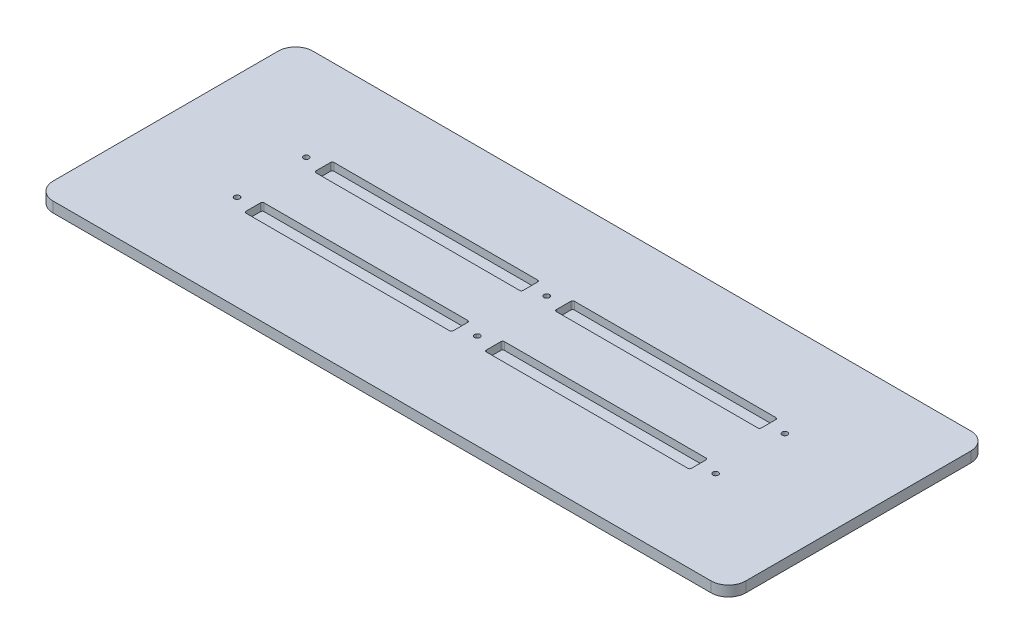
SolidWorks part; units mm, degrees
ref_plane "Ön Düzlem" through (0, 0, 0) normal (0, 0, 1) x (1, 0, 0)
ref_plane "Üst Düzlem" through (0, 0, 0) normal (0, 1, 0) x (1, 0, 0)
ref_plane "Sağ Düzlem" through (0, 0, 0) normal (1, 0, 0) x (0, 0, -1)
sketch "Çizim1" plane through (0, 0, 0) normal (0, 1, 0) x (1, 0, 0)
  line L1 (-200, -75) -> (200, -75)
  line L2 (-200, -75) -> (-200, 75)
  line L3 (-200, 75) -> (200, 75)
  line L4 (200, -75) -> (200, 75)
  line L5 (-200, -75) -> (200, 75) construction
  line L6 (-200, 75) -> (200, -75) construction
  point P0 (0, 0)
  dimension "D1" = 400
  dimension "D2" = 150
extrude "Yükseklik-Ekstrüzyon1" add sketch "Çizim1" against normal blind 6
sketch "Çizim2" plane through (0, 0, 0) normal (0, 1, 0) x (1, 0, 0)
  line L0 (-200, 0) -> (200, 0) construction
  line L1 (-200, 75) -> (-200, -75) construction
  line L2 (200, -75) -> (200, 75) construction
  line L3 (127.99, -15) -> (147.19, -25.4) construction
  line L4 (200, 75) -> (-200, 75) construction
  line L5 (0, 75) -> (0, -75) construction
  line L6 (-200, -75) -> (200, -75) construction
  line L7 (-9.6, 25.4) -> (9.6, 25.4) construction
  line L8 (-9.6, 25.4) -> (-9.6, 15) construction
  line L9 (-9.6, 15) -> (9.6, 15) construction
  line L10 (9.6, 25.4) -> (9.6, 15) construction
  line L11 (-9.6, 25.4) -> (9.6, 15) construction
  line L12 (-9.6, 15) -> (9.6, 25.4) construction
  line L13 (-148.4, 25.4) -> (-129.2, 25.4) construction
  line L14 (-148.4, 25.4) -> (-148.4, 15) construction
  line L15 (-148.4, 15) -> (-129.2, 15) construction
  line L16 (-129.2, 25.4) -> (-129.2, 15) construction
  line L17 (-148.4, 25.4) -> (-129.2, 15) construction
  line L18 (-148.4, 15) -> (-129.2, 25.4) construction
  line L19 (127.99, 25.4) -> (147.19, 25.4) construction
  line L20 (127.99, 25.4) -> (127.99, 15) construction
  line L21 (127.99, 15) -> (147.19, 15) construction
  line L22 (147.19, 25.4) -> (147.19, 15) construction
  line L23 (127.99, 25.4) -> (147.19, 15) construction
  line L24 (127.99, 15) -> (147.19, 25.4) construction
  line L25 (127.99, -25.4) -> (147.19, -15) construction
  line L26 (147.19, -25.4) -> (147.19, -15) construction
  line L27 (127.99, -15) -> (147.19, -15) construction
  line L28 (127.99, -25.4) -> (127.99, -15) construction
  line L29 (127.99, -25.4) -> (147.19, -25.4) construction
  line L30 (-9.6, -15) -> (9.6, -25.4) construction
  line L31 (-9.6, -25.4) -> (9.6, -15) construction
  line L32 (9.6, -25.4) -> (9.6, -15) construction
  line L33 (-9.6, -15) -> (9.6, -15) construction
  line L34 (-9.6, -25.4) -> (-9.6, -15) construction
  line L35 (-9.6, -25.4) -> (9.6, -25.4) construction
  line L36 (-148.4, -15) -> (-129.2, -25.4) construction
  line L37 (-148.4, -25.4) -> (-129.2, -15) construction
  line L38 (-129.2, -25.4) -> (-129.2, -15) construction
  line L39 (-148.4, -15) -> (-129.2, -15) construction
  line L40 (-148.4, -25.4) -> (-148.4, -15) construction
  line L41 (-148.4, -25.4) -> (-129.2, -25.4) construction
  line L43 (-129.2, 25.4) -> (-9.6, 25.4)
  line L44 (-129.2, 25.4) -> (-129.2, 15)
  line L45 (-129.2, 15) -> (-9.6, 15)
  line L46 (-9.6, 25.4) -> (-9.6, 15)
  line L47 (-129.2, -15) -> (-9.6, -15)
  line L48 (-129.2, -15) -> (-129.2, -25.4)
  line L49 (-129.2, -25.4) -> (-9.6, -25.4)
  line L50 (-9.6, -15) -> (-9.6, -25.4)
  line L51 (9.6, 25.4) -> (127.99, 25.4)
  line L52 (9.6, 25.4) -> (9.6, 15)
  line L53 (9.6, 15) -> (127.99, 15)
  line L54 (127.99, 25.4) -> (127.99, 15)
  line L55 (127.99, -15) -> (9.6, -15)
  line L56 (127.99, -15) -> (127.99, -25.4)
  line L57 (127.99, -25.4) -> (9.6, -25.4)
  line L58 (9.6, -15) -> (9.6, -25.4)
  point P12 (0, 20.2)
  point P17 (-138.8, 20.2)
  point P22 (137.59, 20.2)
  point P31 (137.59, -20.2)
  point P36 (0, -20.2)
  point P41 (-138.8, -20.2)
  dimension "D1" = 10.4
  dimension "D2" = 15
  dimension "D3" = 19.2
  dimension "D4" = 19.2
  dimension "D5" = 19.2
  dimension "D6" = 138.8
  dimension "D7" = 137.59
extrude "Kes-Ekstrüzyon1" cut sketch "Çizim2" against normal blind 4.4
fillet "Radyus1" radius 10 4 edges at (200, -3, -75) (200, -3, 75) (-200, -3, 75) (-200, -3, -75)
sketch "Çizim3" plane through (0, -6, 0) normal (0, -1, 0) x (1, 0, 0)
  line L0 (-200, 0) -> (200, 0) construction
  line L1 (-200, -65) -> (-200, 65) construction
  line L2 (200, 65) -> (200, -65) construction
  line L3 (-200, -20) -> (200, -20) construction
  line L4 (-190, 75) -> (190, 75) construction
  line L5 (0, 75) -> (0, -75) construction
  line L6 (190, -75) -> (-190, -75) construction
  line L7 (-138.8, 0) -> (-138.8, -75) construction
  line L9 (137.59, 0) -> (137.59, -75) construction
  circle A0 centre (-138.8, 20) radius 1.575
  circle A1 centre (0, 20) radius 1.575
  circle A2 centre (137.59, 20) radius 1.575
  circle A3 centre (137.59, -20) radius 1.575
  circle A4 centre (0, -20) radius 1.575
  circle A5 centre (-138.8, -20) radius 1.575
  point P18 (137.59, -20)
  point P19 (-138.8, -20)
  point P20 (0, -20)
  point P21 (137.59, 20)
  point P22 (0, 20)
  point P23 (-138.8, 20)
  dimension "D4" = 3.15
  dimension "D1" = 20
  dimension "D2" = 138.8
  dimension "D3" = 137.59
extrude "Kes-Ekstrüzyon2" cut sketch "Çizim3" against normal through all
sketch "Çizim4" plane through (0, -6, 0) normal (0, -1, 0) x (1, 0, 0)
  line L0 (-200, 0) -> (200, 0) construction
  line L1 (-200, -65) -> (-200, 65) construction
  line L2 (200, 65) -> (200, -65) construction
  circle A0 centre (-138.8, 20) radius 2.75
  circle A1 centre (0, 20) radius 2.75
  circle A2 centre (137.59, 20) radius 2.75
  circle A3 centre (137.59, 20) radius 1.575 construction
  circle A4 centre (0, 20) radius 1.575 construction
  circle A5 centre (-138.8, 20) radius 1.575 construction
  circle A6 centre (137.59, -20) radius 2.75
  circle A7 centre (0, -20) radius 2.75
  circle A8 centre (-138.8, -20) radius 2.75
  dimension "D1" = 5.5
extrude "Kes-Ekstrüzyon3" cut sketch "Çizim4" against normal blind 2.89
fillet "Radyus2" radius 1 16 edges at (-129.2, -2.2, 15) (-9.6, -2.2, 15) (-9.6, -2.2, 25.4) (9.6, -2.2, 25.4) (9.6, -2.2, 15) (127.99, -2.2, 15) (127.99, -2.2, 25.4) (127.99, -2.2, -15) (-9.6, -2.2, -15) (-129.2, -2.2, 25.4) (-129.2, -2.2, -15) (9.6, -2.2, -15) (9.6, -2.2, -25.4) (127.99, -2.2, -25.4) (-9.6, -2.2, -25.4) (-129.2, -2.2, -25.4)
